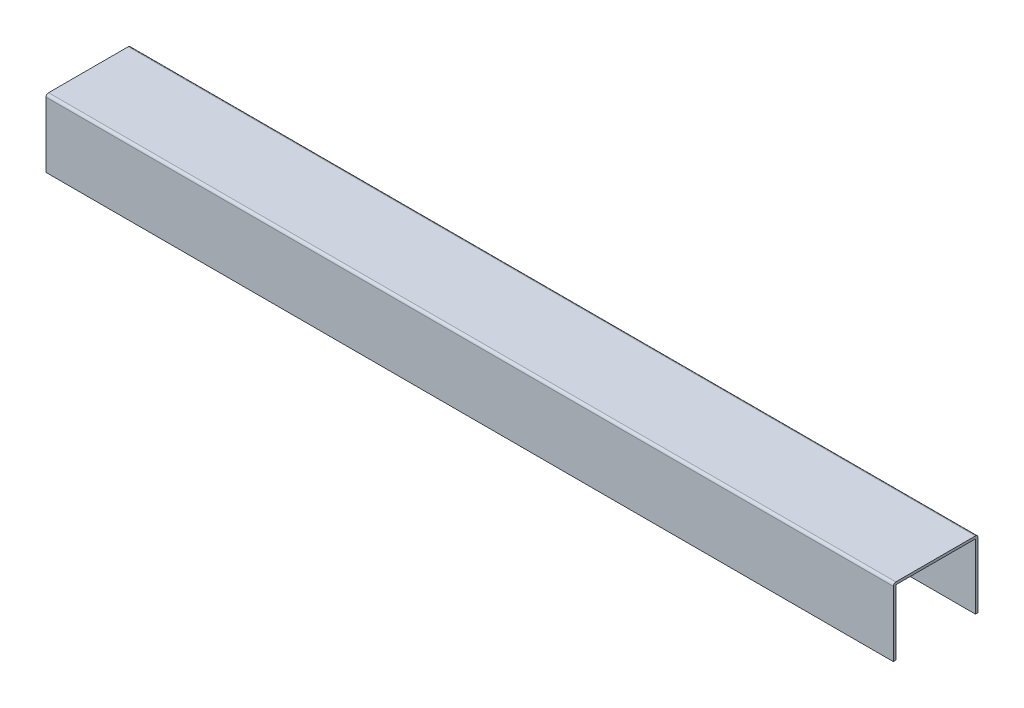
SolidWorks part; units mm, degrees
ref_plane "Спереди" through (0, 0, 0) normal (0, 0, 1) x (1, 0, 0)
ref_plane "Сверху" through (0, 0, 0) normal (0, 1, 0) x (1, 0, 0)
ref_plane "Справа" through (0, 0, 0) normal (1, 0, 0) x (0, 0, -1)
sketch "Эскиз1" plane through (0, 0, 0) normal (1, 0, 0) x (0, 0, -1)
  line L1 (3, 0) -> (97, 0)
  line L2 (0, 3) -> (0, 97)
  line L3 (3, 100) -> (97, 100)
  line L4 (100, 3) -> (100, 97)
  arc A0 (0, 3) -> (3, 0) centre (3, 3) ccw
  arc A1 (97, 0) -> (100, 3) centre (97, 3) ccw
  arc A2 (97, 100) -> (100, 97) centre (97, 97) cw
  arc A3 (0, 97) -> (3, 100) centre (3, 97) cw
  point P7 (0, 0)
  dimension "D1" = 3
extrude "Вытянуть-Тонкостенный1" add sketch "Эскиз1" along normal blind 1000 thin
sketch "Эскиз2" plane through (0, 0, -100) normal (0, 0, -1) x (-1, 0, 0)
  line L0 (-1000, 3) -> (-1000, 97) construction
  line L1 (-1000, 20) -> (0, 20)
  line L2 (-1000, 20) -> (-1000, 0)
  line L3 (-1000, 0) -> (0, 0)
  line L4 (0, 20) -> (0, 0)
extrude "Вырез-Вытянуть1" cut sketch "Эскиз2" against normal through all
